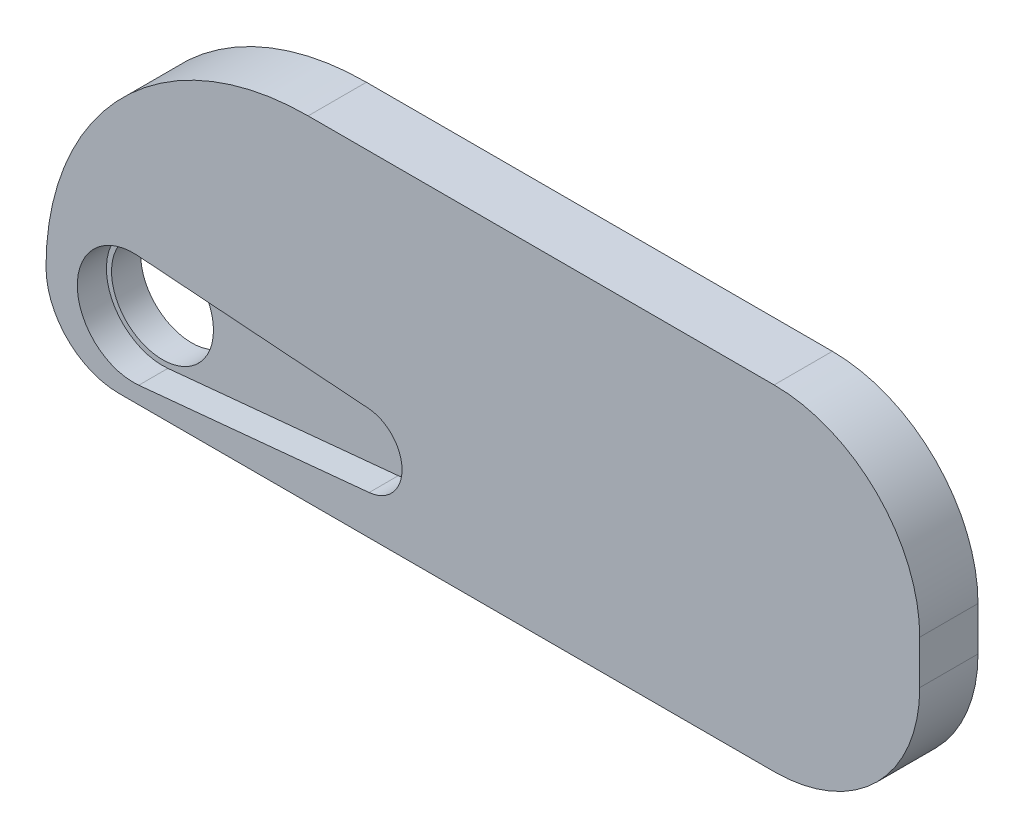
SolidWorks part; units mm, degrees
ref_plane "Ebene vorne" through (0, 0, 0) normal (0, 0, 1) x (1, 0, 0)
ref_plane "Ebene oben" through (0, 0, 0) normal (0, 1, 0) x (1, 0, 0)
ref_plane "Ebene rechts" through (0, 0, 0) normal (1, 0, 0) x (0, 0, -1)
sketch "Skizze6" plane through (0, 0, 0) normal (0, 0, 1) x (1, 0, 0)
  line L1 (0, 18) -> (60, 18)
  line L2 (0, 18) -> (0, -5)
  line L3 (0, -5) -> (60, -5)
  line L4 (60, 18) -> (60, -5)
  dimension "D1" = 5
  dimension "D2" = 18
  dimension "D3" = 60
extrude "Aufsatz-Linear austragen1" add sketch "Skizze6" along normal blind 4
sketch "Skizze7" plane through (0, 0, 4) normal (0, 0, 1) x (1, 0, 0)
  line L0 (0, 0) -> (6, 0) construction
  line L1 (2.5, 6.2224) -> (2.5, -6.5906) construction
  line L2 (0, 18) -> (0, -5) construction
  circle A0 centre (6, 0) radius 3.5
  dimension "D1" = 7
  dimension "D2" = 2.5
extrude "Schnitt-Linear austragen1" cut sketch "Skizze7" against normal through all
fillet "Verrundung1" radius 10 3 edges at (60, 18, 2) (60, -5, 2) (0, 18, 2)
sketch "Skizze9" plane through (0, 0, 4) normal (0, 0, 1) x (1, 0, 0)
  line L0 (6.2816, 3.8397) -> (22.1318, 2.6774)
  line L1 (22.1893, -2.3043) -> (6.3701, -3.8322)
  line L2 (6.245, 3.341) -> (22.0952, 2.1788) construction
  arc A0 (6.2816, 3.8397) -> (6.3701, -3.8322) centre (6, 0) ccw
  arc A1 (22.1318, 2.6774) -> (22.1893, -2.3043) centre (21.9489, 0.1841) cw
  arc A3 (6.245, 3.341) -> (6.3221, -3.3345) centre (6, 0) ccw construction
  dimension "D1" = 0.5
extrude "Schnitt-Linear austragen2" cut sketch "Skizze9" against normal blind 2
fillet "Verrundung2" radius 5 1 edges at (0, -5, 2)
sketch "Skizze10" plane through (0, 0, 4) normal (0, 0, 1) x (1, 0, 0)
  line L4 (50, 18) -> (10, 18) construction
  line L6 (18, 18) -> (0, 18)
  line L7 (0, 18) -> (0, 0)
  line L8 (0, 8) -> (0, 0) construction
  arc A1 (18, 18) -> (0, 0) centre (18, 0) ccw
extrude "Schnitt-Linear austragen3" cut sketch "Skizze10" against normal through all
